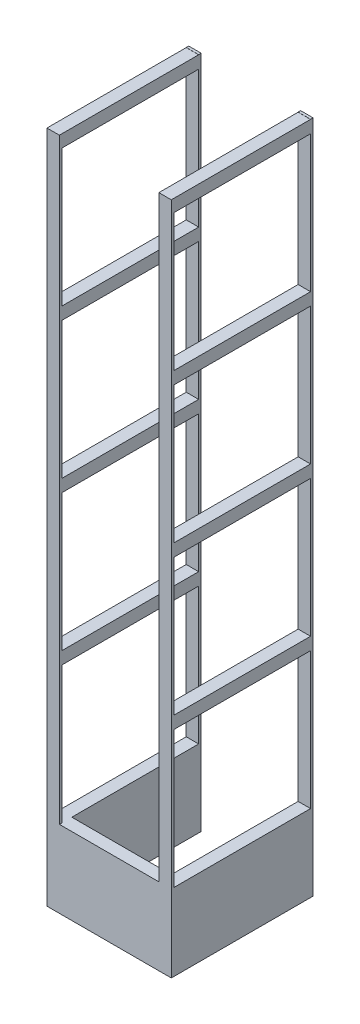
SolidWorks part; units mm, degrees
ref_plane "Front Plane" through (0, 0, 0) normal (0, 0, 1) x (1, 0, 0)
ref_plane "Top Plane" through (0, 0, 0) normal (0, 1, 0) x (1, 0, 0)
ref_plane "Right Plane" through (0, 0, 0) normal (1, 0, 0) x (0, 0, -1)
sketch "Sketch1" plane through (0, 0, 0) normal (0, 0, 1) x (1, 0, 0)
  line L1 (-5, -1) -> (5, -1)
  line L2 (-5, -1) -> (-5, 1)
  line L3 (-5, 1) -> (5, 1)
  line L4 (5, -1) -> (5, 1)
  line L5 (-5, -1) -> (5, 1) construction
  line L6 (-5, 1) -> (5, -1) construction
  point P0 (0, 0)
  dimension "D1" = 2
  dimension "D2" = 10
extrude "Boss-Extrude1" add sketch "Sketch1" along normal blind 112
sketch "Sketch2" plane through (0, 1, 0) normal (0, 1, 0) x (1, 0, 0)
  line L0 (5, -112) -> (5, 0) construction
  line L1 (-5, -112) -> (5, -112)
  line L2 (-5, -112) -> (-5, -110)
  line L3 (-5, -110) -> (5, -110)
  line L4 (5, -112) -> (5, -110)
  dimension "D1" = 2
extrude "Boss-Extrude2" add sketch "Sketch2" along normal blind 480
sketch "Sketch3" plane through (5, 0, 0) normal (1, 0, 0) x (0, 0, -1)
  line L0 (-110, 1) -> (0, 1) construction
  line L1 (-112, -1) -> (-102, -1)
  line L2 (-112, -1) -> (-112, 1)
  line L3 (-112, 1) -> (-102, 1)
  line L4 (-102, -1) -> (-102, 1)
  dimension "D1" = 10
extrude "Boss-Extrude3" add sketch "Sketch3" along normal blind 90
sketch "Sketch4" plane through (0, 0, 102) normal (0, 0, -1) x (-1, 0, 0)
  line L0 (-95, -1) -> (-5, -1) construction
  line L1 (-95, 1) -> (-85, 1)
  line L2 (-95, 1) -> (-95, -1)
  line L3 (-95, -1) -> (-85, -1)
  line L4 (-85, 1) -> (-85, -1)
  dimension "D1" = 10
extrude "Boss-Extrude4" add sketch "Sketch4" along normal blind 102
sketch "Sketch5" plane through (0, 1, 0) normal (0, 1, 0) x (1, 0, 0)
  line L1 (95, -112) -> (85, -112)
  line L2 (95, -112) -> (95, -110)
  line L3 (95, -110) -> (85, -110)
  line L4 (85, -112) -> (85, -110)
  dimension "D1" = 2
  dimension "D2" = 10
extrude "Boss-Extrude5" add sketch "Sketch5" along normal blind 480
sketch "Sketch6" plane through (0, 0, 110) normal (0, 0, -1) x (-1, 0, 0)
  line L0 (-95, 1) -> (-95, 111) construction
  line L1 (-95, 481) -> (-95, 1) construction
  line L2 (5, 481) -> (5, 1) construction
  line L3 (-95, 111) -> (5, 111)
  line L4 (-95, 111) -> (-95, 121)
  line L5 (-95, 121) -> (5, 121)
  line L6 (5, 111) -> (5, 121)
  line L7 (-85, 121) -> (-85, 111)
  line L8 (-85, 481) -> (-85, 1) construction
  line L9 (-5, 121) -> (-5, 111)
  line L10 (-5, 481) -> (-5, 1) construction
  line M4 (-85, 1) -> (-85, 481)
  line M6 (-95, 481) -> (-95, 1)
  dimension "D1" = 110
  dimension "D2" = 10
extrude "Boss-Extrude6" add sketch "Sketch6" along normal blind 110 contours L5 L3 M6 M4 | L5 L9 L3 L6
sketch "Sketch7" plane through (0, 0, 110) normal (0, 0, -1) x (-1, 0, 0)
  line L0 (-95, 121) -> (-95, 231) construction
  line L1 (-95, 481) -> (-95, 121) construction
  line L2 (5, 481) -> (5, 121) construction
  line L3 (-95, 231) -> (5, 231)
  line L4 (-95, 231) -> (-95, 241)
  line L5 (-95, 241) -> (5, 241)
  line L6 (5, 231) -> (5, 241)
  line L7 (-85, 241) -> (-85, 231)
  line L8 (-85, 481) -> (-85, 121) construction
  line L9 (-5, 241) -> (-5, 231)
  line L10 (-5, 481) -> (-5, 121) construction
  line M3 (-95, 481) -> (-95, 121)
  line M5 (-85, 121) -> (-85, 481)
  dimension "D1" = 110
  dimension "D2" = 10
extrude "Boss-Extrude7" add sketch "Sketch7" along normal blind 110 contours L5 L3 M3 M5 | L5 L9 L3 L6
sketch "Sketch8" plane through (0, 0, 110) normal (0, 0, -1) x (-1, 0, 0)
  line L0 (-95, 241) -> (-95, 351)
  line L1 (5, 481) -> (5, 241) construction
  line L2 (-95, 351) -> (5, 351)
  line L3 (-95, 351) -> (-95, 361)
  line L4 (-95, 361) -> (5, 361)
  line L5 (5, 351) -> (5, 361)
  line L6 (-85, 361) -> (-85, 351)
  line L7 (-85, 481) -> (-85, 241) construction
  line L8 (-5, 361) -> (-5, 351)
  line L9 (-5, 481) -> (-5, 241) construction
  line M2 (-95, 481) -> (-95, 241)
  line M4 (-85, 241) -> (-85, 481)
  dimension "D1" = 110
  dimension "D2" = 10
extrude "Boss-Extrude8" add sketch "Sketch8" along normal blind 110 contours L4 L2 M2 M4 | L4 L8 L2 L5
sketch "Sketch9" plane through (0, 0, 110) normal (0, 0, -1) x (-1, 0, 0)
  line L0 (-95, 361) -> (-95, 471) construction
  line L1 (-85, 481) -> (-85, 471)
  line L2 (-95, 471) -> (5, 471)
  line L3 (-95, 471) -> (-95, 481)
  line L4 (-95, 481) -> (5, 481)
  line L5 (5, 471) -> (5, 481)
  line L6 (-85, 481) -> (-85, 361) construction
  line L7 (-5, 481) -> (-5, 471)
  line L8 (-5, 481) -> (-5, 361) construction
  line M2 (-95, 481) -> (-95, 361)
  line M4 (-85, 361) -> (-85, 481)
  line M5 (-85, 481) -> (-95, 481)
  dimension "D1" = 110
extrude "Boss-Extrude9" add sketch "Sketch9" along normal blind 110 contours L2 M2 M4 M5 | L4 L7 L2 L5
sketch "Sketch11" plane through (0, -1, 0) normal (0, -1, 0) x (1, 0, 0)
  line L1 (-5, 112) -> (95, 112)
  line L2 (-5, 112) -> (-5, 0)
  line L3 (-5, 0) -> (95, 0)
  line L4 (95, 112) -> (95, 0)
  line L5 (5, 0) -> (85, 0)
  line L6 (5, 0) -> (5, 102)
  line L7 (5, 102) -> (85, 102)
  line L8 (85, 0) -> (85, 102)
  line M1 (-5, 0) -> (5, 0)
  line M2 (5, 0) -> (5, 102)
  line M3 (5, 102) -> (85, 102)
  line M4 (85, 102) -> (85, 0)
  line M5 (85, 0) -> (95, 0)
  line M6 (95, 0) -> (95, 112)
  line M7 (95, 112) -> (-5, 112)
  line M8 (-5, 112) -> (-5, 0)
extrude "Boss-Extrude10" add sketch "Sketch11" along normal blind 60 contours M8 M1 M2 M3 M4 M5 M6 M7
sketch "Sketch12" plane through (0, -61, 0) normal (0, -1, 0) x (1, 0, 0)
  line L1 (-5, 0) -> (95, 0)
  line L2 (-5, 0) -> (-5, -2)
  line L3 (-5, -2) -> (95, -2)
  line L4 (95, 0) -> (95, -2)
  line L9 (5, 0) -> (85, 0)
  line L10 (5, 0) -> (5, -2)
  line L11 (5, -2) -> (85, -2)
  line L12 (85, 0) -> (85, -2)
  line M10 (-5, 0) -> (5, 0)
  line M14 (85, 0) -> (95, 0)
  dimension "D1" = 2
extrude "Boss-Extrude11" add sketch "Sketch12" against normal blind 542.1162 contours L12 L3 L4 M14 | L10 L2 L3 M10
